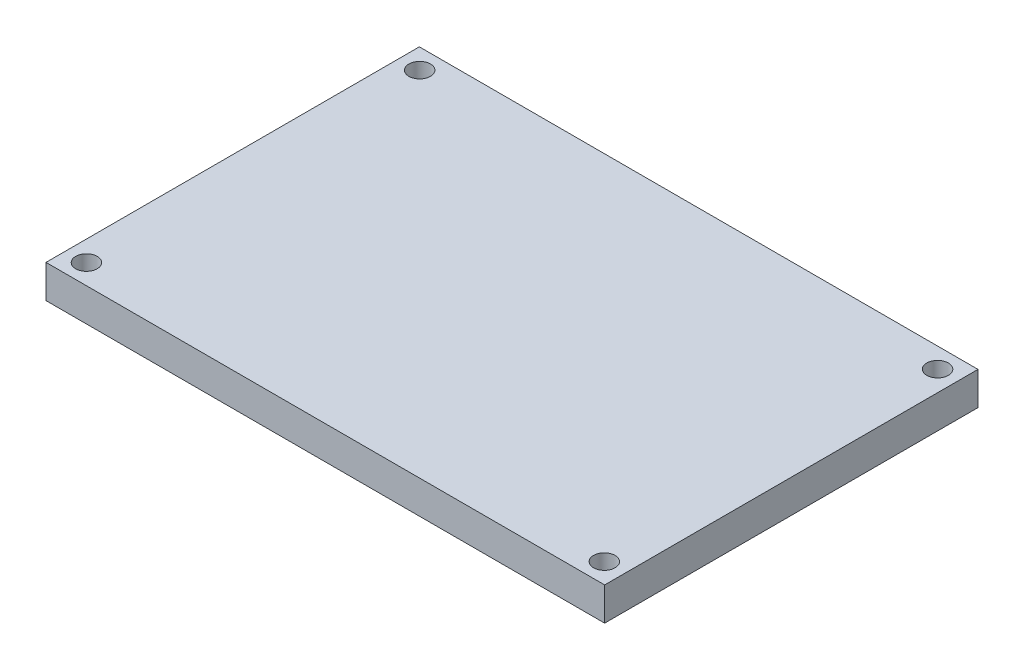
SolidWorks part; units mm, degrees
ref_plane "Front Plane" through (0, 0, 0) normal (0, 0, 1) x (1, 0, 0)
ref_plane "Top Plane" through (0, 0, 0) normal (0, 1, 0) x (1, 0, 0)
ref_plane "Right Plane" through (0, 0, 0) normal (1, 0, 0) x (0, 0, -1)
sketch "Sketch1" plane through (0, 0, 0) normal (0, 1, 0) x (1, 0, 0)
  line L0 (-1000, 0) -> (49000, 0) construction
  line L1 (-42.16, -28.175) -> (42.16, -28.175)
  line L2 (-42.16, -28.175) -> (-42.16, 28.175)
  line L3 (-42.16, 28.175) -> (42.16, 28.175)
  line L4 (42.16, -28.175) -> (42.16, 28.175)
  line L5 (-42.16, -28.175) -> (42.16, 28.175) construction
  line L6 (-42.16, 28.175) -> (42.16, -28.175) construction
  line L7 (0, -1000) -> (0, 49000) construction
  circle A0 centre (39.085, 25.15) radius 1.625
  circle A1 centre (-39.085, 25.15) radius 1.625
  circle A2 centre (-39.085, -25.15) radius 1.625
  circle A3 centre (39.085, -25.15) radius 1.625
  point P0 (0, 0)
  dimension "D3" = 3.25
  dimension "D5" = 3.025
  dimension "D1" = 84.32
  dimension "D2" = 56.35
  dimension "D4" = 3.075
extrude "Boss-Extrude1" add sketch "Sketch1" along normal blind 5
